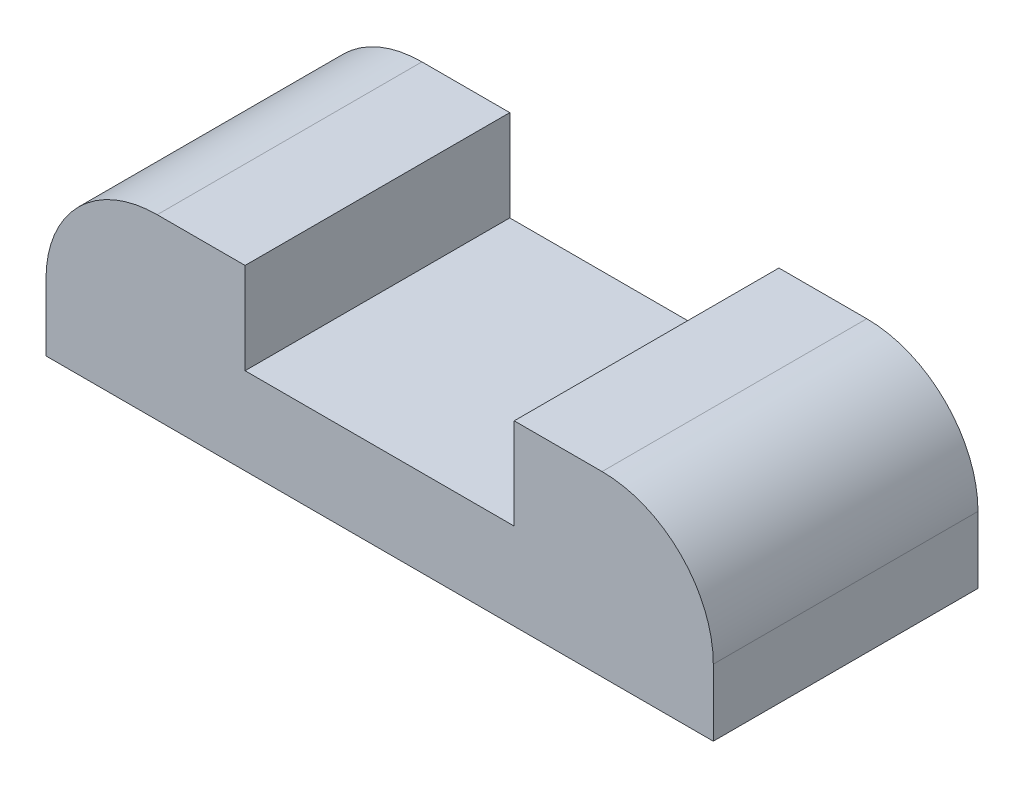
SolidWorks part; units mm, degrees
ref_plane "Front Plane" through (0, 0, 0) normal (0, 0, 1) x (1, 0, 0)
ref_plane "Top Plane" through (0, 0, 0) normal (0, 1, 0) x (1, 0, 0)
ref_plane "Right Plane" through (0, 0, 0) normal (1, 0, 0) x (0, 0, -1)
sketch "Sketch1" plane through (0, 0, 0) normal (0, 1, 0) x (1, 0, 0)
  line L0 (-15, -5.95) -> (15, 5.95) construction
  line L1 (-15, 5.95) -> (15, 5.95)
  line L2 (-15, 5.95) -> (-15, -5.95)
  line L3 (-15, -5.95) -> (15, -5.95)
  line L4 (15, 5.95) -> (15, -5.95)
  point P4 (0, 0)
  dimension "D1" = 30
  dimension "D2" = 11.9
extrude "Boss-Extrude1" add sketch "Sketch1" along normal blind 8
sketch "Sketch3" plane through (0, 8, 0) normal (0, 1, 0) x (1, 0, 0)
  line L0 (15, 5.95) -> (-15, 5.95) construction
  line L1 (-6.05, 5.95) -> (6.05, 5.95)
  line L2 (-6.05, 5.95) -> (-6.05, -5.95)
  line L3 (-6.05, -5.95) -> (6.05, -5.95)
  line L4 (6.05, 5.95) -> (6.05, -5.95)
  line L5 (-15, -5.95) -> (15, -5.95) construction
  line L6 (-6.05, -5.95) -> (6.05, 5.95) construction
  point P8 (0, 0)
  dimension "D1" = 12.1
extrude "Cut-Extrude1" cut sketch "Sketch3" against normal blind 4.1
fillet "Fillet1" radius 5 2 edges at (-15, 8, 0) (15, 8, 0)
